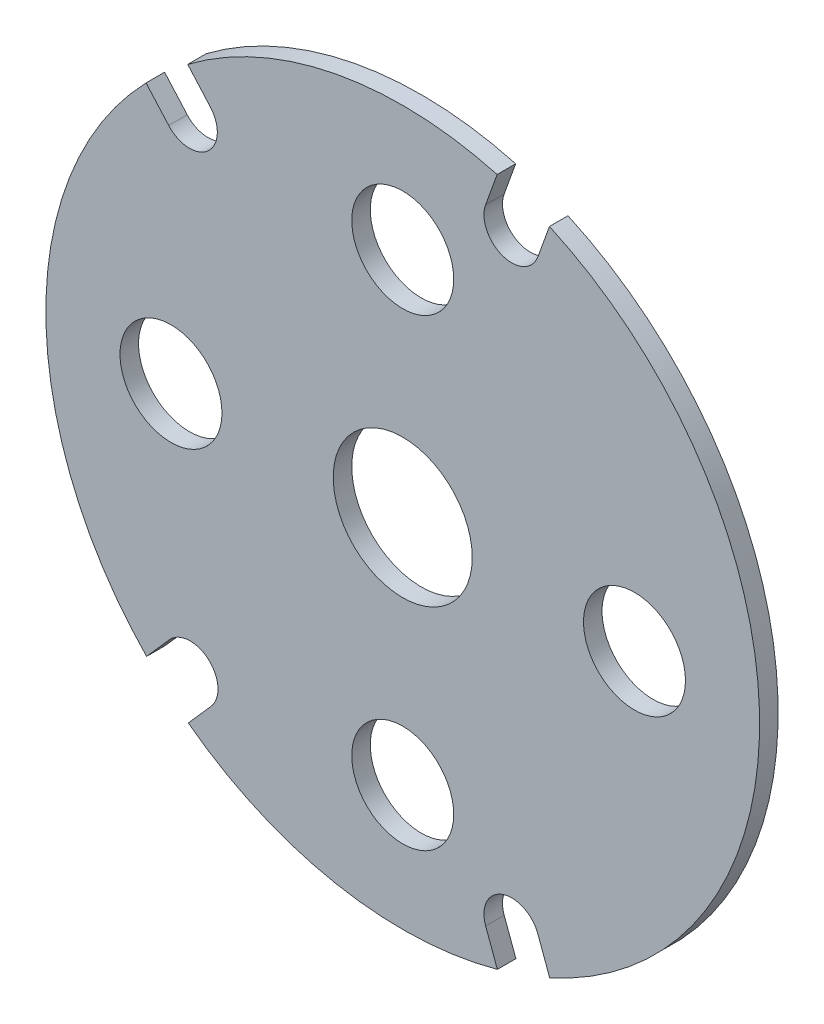
SolidWorks part; units mm, degrees
material "Acrylic (Medium-high impact)"
ref_plane "Front Plane" through (0, 0, 0) normal (0, 0, 1) x (1, 0, 0)
ref_plane "Top Plane" through (0, 0, 0) normal (0, 1, 0) x (1, 0, 0)
ref_plane "Right Plane" through (0, 0, 0) normal (1, 0, 0) x (0, 0, -1)
sketch "Model" plane through (0, 0, 0) normal (0, 0, 1) x (1, 0, 0)
  line L0 (8.9473, -33.6974) -> (10.207, -37.1223)
  line L1 (14.5854, 31.6454) -> (15.828, 35.0959)
  line L2 (14.5784, -31.6263) -> (15.8508, -35.0856)
  line L3 (8.9404, 33.6784) -> (10.1831, 37.1289)
  line L8 (-23.1958, 30.7279) -> (-20.7537, 27.9693)
  line L9 (-27.6884, 26.7508) -> (-25.2463, 23.9922)
  line L12 (-23.1353, -30.7735) -> (-20.6815, -27.9907)
  line L13 (-27.6357, -26.8052) -> (-25.1819, -24.0224)
  arc A0 (-23.1958, 30.7279) -> (10.1831, 37.1289) centre (0, 0) cw
  arc A1 (-23.1353, -30.7735) -> (10.207, -37.1223) centre (0, 0) ccw
  circle A7 centre (-25, 0) radius 5.5
  arc A15 (-25.2463, 23.9922) -> (-20.7537, 27.9693) centre (-23, 25.9808) ccw
  arc A16 (-20.6815, -27.9907) -> (-25.1819, -24.0224) centre (-22.9317, -26.0066) ccw
  circle A17 centre (0, 25) radius 5.5
  circle A18 centre (0, -25) radius 5.5
  circle A19 centre (25, 0) radius 5.5
  circle A20 centre (0, 0) radius 7.5
  arc A21 (8.9404, 33.6784) -> (14.5854, 31.6454) centre (11.7629, 32.6619) ccw
  arc A22 (-27.6884, 26.7508) -> (-27.6357, -26.8052) centre (0, 0) ccw
  arc A23 (14.5784, -31.6263) -> (8.9473, -33.6974) centre (11.7629, -32.6619) ccw
  arc A24 (15.8508, -35.0856) -> (15.828, 35.0959) centre (0, 0) ccw
  dimension "D1" = 11
  dimension "D2" = 15
  dimension "D3" = 38.5
  dimension "D4" = 3
  dimension "D5" = 3
  dimension "D6" = 8.9404
  dimension "D7" = 8.9473
  dimension "D8" = 10.1831
  dimension "D9" = 10.207
  dimension "D10" = 11.7629
  dimension "D11" = 14.5784
  dimension "D12" = 25
  dimension "D13" = 20.6815
  dimension "D14" = 20.7537
  dimension "D15" = 22.9317
  dimension "D16" = 23
  dimension "D17" = 23.1353
  dimension "D18" = 23.1958
  dimension "D19" = 25
  dimension "D20" = 25
  dimension "D21" = 25
extrude "Boss-Extrude1" add sketch "Model" along normal blind 2
